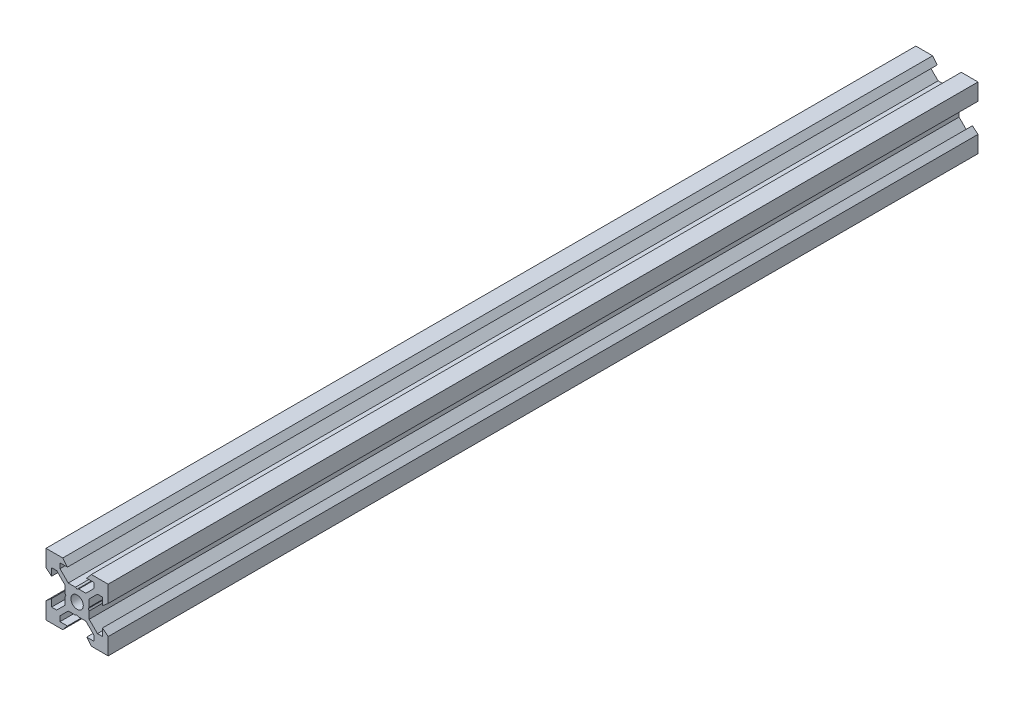
SolidWorks part; units mm, degrees
ref_plane "Front Plane" through (0, 0, 0) normal (0, 0, 1) x (1, 0, 0)
ref_plane "Top Plane" through (0, 0, 0) normal (0, 1, 0) x (1, 0, 0)
ref_plane "Right Plane" through (0, 0, 0) normal (1, 0, 0) x (0, 0, -1)
sketch "Sketch1" plane through (0, 0, 0) normal (0, 0, 1) x (1, 0, 0)
  line L0 (10, 10) -> (4.6104, 10) construction
  line L1 (10, 10) -> (10, 4.6104) construction
  line L2 (10, -10) -> (10, -4.6104) construction
  line L3 (10, -10) -> (4.6104, -10) construction
  line L4 (10, 10) -> (10, 4.6104)
  line L5 (6.5607, 5.5) -> (8.2, 5.5)
  line L6 (5.5, 8.2) -> (5.5, 6.5607)
  line L7 (10, 10) -> (4.6104, 10)
  line L8 (10, 10) -> (10, 4.6104)
  line L9 (6.5607, 5.5) -> (3.9, 2.8393)
  line L10 (5.5, 6.5607) -> (2.8393, 3.9)
  line L11 (10, 4.6104) -> (8.2, 3.1)
  line L12 (4.6104, 10) -> (3.1, 8.2)
  line L13 (8.2, 3.1) -> (8.2, 5.5)
  line L14 (3.1, 8.2) -> (5.5, 8.2)
  line L15 (-6.5607, 5.5) -> (-8.2, 5.5)
  line L16 (6.5607, -5.5) -> (8.2, -5.5)
  line L17 (3.1, -8.2) -> (5.5, -8.2)
  line L18 (8.2, -3.1) -> (8.2, -5.5)
  line L19 (4.6104, -10) -> (3.1, -8.2)
  line L20 (10, -4.6104) -> (8.2, -3.1)
  line L21 (0.5196, -3.9) -> (0, -3.6)
  line L22 (0.5196, 3.9) -> (0, 3.6)
  line L23 (3.6, 0) -> (3.9, -0.5196)
  line L24 (3.9, 0.5196) -> (3.6, 0)
  line L25 (3.9, 0.5196) -> (3.9, 2.8393)
  line L26 (2.8393, 3.9) -> (0.5196, 3.9)
  line L27 (3.9, -2.8393) -> (3.9, -0.5196)
  line L28 (2.8393, -3.9) -> (0.5196, -3.9)
  line L29 (5.5, -6.5607) -> (2.8393, -3.9)
  line L30 (6.5607, -5.5) -> (3.9, -2.8393)
  line L31 (10, -10) -> (10, -4.6104)
  line L32 (10, -10) -> (4.6104, -10)
  line L33 (5.5, -8.2) -> (5.5, -6.5607)
  line L34 (-6.5607, -5.5) -> (-8.2, -5.5)
  line L35 (10, -10) -> (10, -4.6104)
  line L36 (0, 0) -> (0, 8.2) construction
  line L37 (-10, -10) -> (-4.6104, -10) construction
  line L38 (-10, -10) -> (-10, -4.6104) construction
  line L39 (-10, 10) -> (-10, 4.6104) construction
  line L40 (-10, 10) -> (-4.6104, 10) construction
  line L41 (-10, -10) -> (-10, -4.6104)
  line L43 (-5.5, -8.2) -> (-5.5, -6.5607)
  line L44 (-10, -10) -> (-4.6104, -10)
  line L45 (-10, -10) -> (-10, -4.6104)
  line L46 (-6.5607, -5.5) -> (-3.9, -2.8393)
  line L47 (-5.5, -6.5607) -> (-2.8393, -3.9)
  line L48 (-2.8393, -3.9) -> (-0.5196, -3.9)
  line L49 (-3.9, -2.8393) -> (-3.9, -0.5196)
  line L50 (-2.8393, 3.9) -> (-0.5196, 3.9)
  line L51 (-3.9, 0.5196) -> (-3.9, 2.8393)
  line L52 (-3.9, 0.5196) -> (-3.6, 0)
  line L53 (-3.6, 0) -> (-3.9, -0.5196)
  line L54 (-0.5196, 3.9) -> (0, 3.6)
  line L55 (-0.5196, -3.9) -> (0, -3.6)
  line L56 (-10, -4.6104) -> (-8.2, -3.1)
  line L57 (-4.6104, -10) -> (-3.1, -8.2)
  line L58 (-8.2, -3.1) -> (-8.2, -5.5)
  line L59 (-3.1, -8.2) -> (-5.5, -8.2)
  line L60 (-10, -10) -> (10, -10) construction
  line L61 (-10, -10) -> (-10, 10) construction
  line L62 (-3.1, 8.2) -> (-5.5, 8.2)
  line L63 (-8.2, 3.1) -> (-8.2, 5.5)
  line L64 (-4.6104, 10) -> (-3.1, 8.2)
  line L65 (-10, 4.6104) -> (-8.2, 3.1)
  line L66 (-5.5, 6.5607) -> (-2.8393, 3.9)
  line L67 (-6.5607, 5.5) -> (-3.9, 2.8393)
  line L68 (-10, 10) -> (-10, 4.6104)
  line L69 (-10, 10) -> (-4.6104, 10)
  line L70 (-5.5, 8.2) -> (-5.5, 6.5607)
  line L71 (-10, 10) -> (10, 10) construction
  line L72 (-10, 10) -> (-10, 4.6104)
  line L73 (10, -10) -> (10, 10) construction
  line L74 (-10, -10) -> (10, 10) construction
  line L75 (-10, 10) -> (10, -10) construction
  circle A0 centre (0, 0) radius 2
  dimension "D7" = 4
  dimension "D1" = 20
  dimension "D2" = 5.3896
  dimension "D3" = 4.5
  dimension "D4" = 50
  dimension "D5" = 1.8
  dimension "D6" = 1.5104
  dimension "D8" = 5.5
  dimension "D9" = 120
  dimension "D10" = 0.3
  dimension "D11" = 2.3197
  dimension "D12" = 7.8
  dimension "D13" = 7.8
  dimension "D14" = 1.5
  dimension "D15" = 2.6607
extrude "Boss-Extrude1" add sketch "Sketch1" along normal mid plane 280 contours L70 L62 L64 L69 L68 L65 L63 L15 L67 L51 L52 L53 L49 L46 L34 L58 L56 L41 L44 L57 L59 L43 L47 L48 L55 L21 L28 L29 L33 L17 L19 L32 L31 L20 L18 L16 L30 L27 L23 L24 L25 L9 L5 L13 L11 L4 L7 L12 L14 L6 L10
